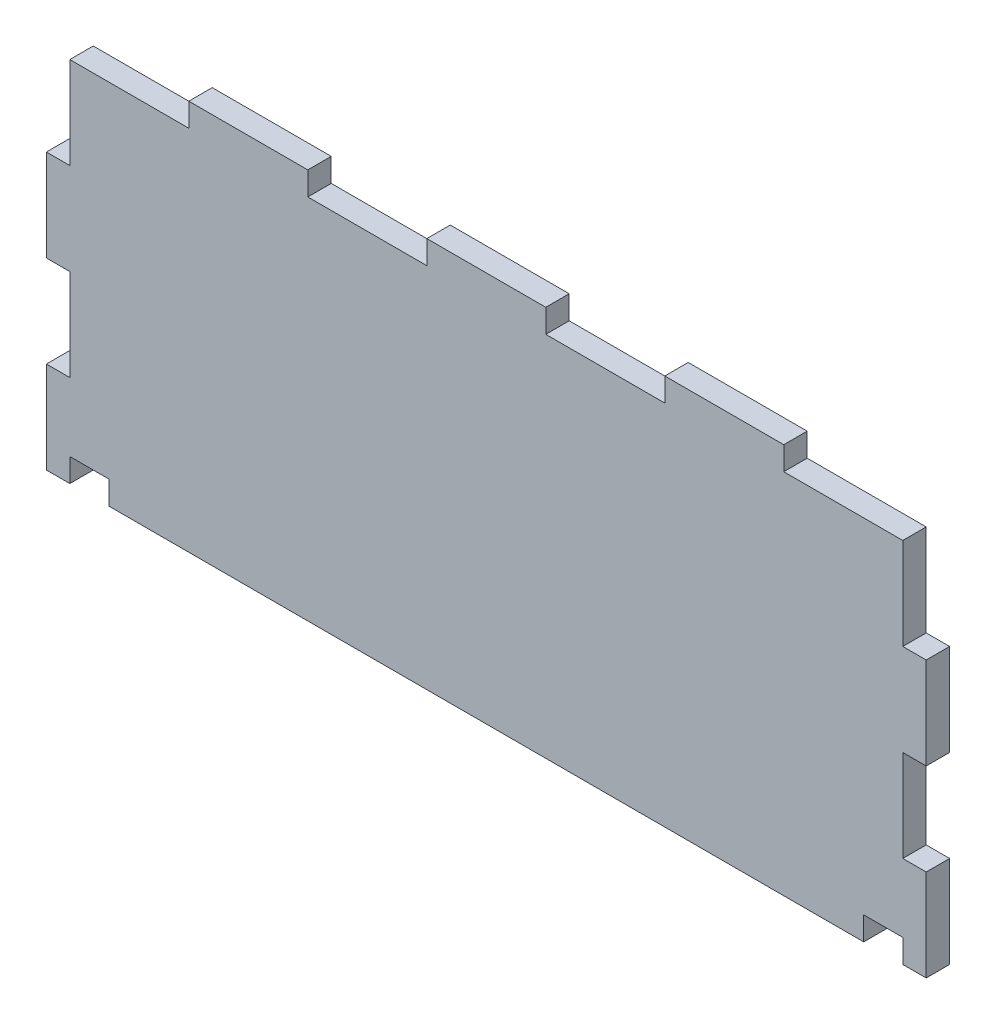
SolidWorks part; units mm, degrees
ref_plane "Alzado" through (0, 0, 0) normal (0, 0, 1) x (1, 0, 0)
ref_plane "Planta" through (0, 0, 0) normal (0, 1, 0) x (1, 0, 0)
ref_plane "Vista lateral" through (0, 0, 0) normal (1, 0, 0) x (0, 0, -1)
sketch "Croquis1" plane through (0, 0, 0) normal (0, 0, 1) x (1, 0, 0)
  line L0 (-76.15, 28.8494) -> (-76.15, -51.02) construction
  line L1 (-79.15, 18.6361) -> (33.46, 18.6361) construction
  line L2 (-79.15, 18.6361) -> (-79.15, -31.3639) construction
  line L3 (-79.15, -31.3639) -> (33.46, -31.3639) construction
  line L4 (33.46, 18.6361) -> (33.46, -31.3639) construction
  line L5 (30.46, 26.8438) -> (30.46, -48.3082) construction
  line L6 (-85.6573, -28.3639) -> (41.9564, -28.3639) construction
  line L7 (-99.0946, 15.6361) -> (68.6346, 15.6361) construction
  line L8 (-71.15, -28.3639) -> (-71.15, -31.3639)
  line L9 (25.46, -28.3639) -> (25.46, -31.3639)
  line L10 (-71.15, -31.3639) -> (25.46, -31.3639)
  line L11 (-71.15, -28.3639) -> (-76.15, -28.3639)
  line L12 (-76.15, -28.3639) -> (-76.15, -31.3639)
  line L13 (-76.15, -31.3639) -> (-79.15, -31.3639)
  line L14 (25.46, -28.3639) -> (30.46, -28.3639)
  line L15 (30.46, -28.3639) -> (30.46, -31.3639)
  line L16 (30.46, -31.3639) -> (33.46, -31.3639)
  line L17 (33.46, -31.3639) -> (33.46, -19.6139)
  line L18 (33.46, -19.6139) -> (30.46, -19.6139)
  line L19 (30.46, -19.6139) -> (30.46, -7.8639)
  line L20 (30.46, -7.8639) -> (33.46, -7.8639)
  line L21 (33.46, -7.8639) -> (33.46, 3.8861)
  line L22 (33.46, 3.8861) -> (30.46, 3.8861)
  line L23 (30.46, 3.8861) -> (30.46, 15.6361)
  line L24 (30.46, 15.6361) -> (15.23, 15.6361)
  line L25 (15.23, 15.6361) -> (15.23, 18.6361)
  line L26 (15.23, 18.6361) -> (0, 18.6361)
  line L27 (0, 18.6361) -> (0, 15.6361)
  line L28 (0, 15.6361) -> (-15.23, 15.6361)
  line L29 (-15.23, 15.6361) -> (-15.23, 18.6361)
  line L30 (-15.23, 18.6361) -> (-30.46, 18.6361)
  line L31 (-30.46, 18.6361) -> (-30.46, 15.6361)
  line L32 (-30.46, 15.6361) -> (-45.69, 15.6361)
  line L33 (-45.69, 15.6361) -> (-45.69, 18.6361)
  line L34 (-45.69, 18.6361) -> (-60.92, 18.6361)
  line L35 (-60.92, 18.6361) -> (-60.92, 15.6361)
  line L36 (-60.92, 15.6361) -> (-76.15, 15.6361)
  line L37 (-79.15, -31.3639) -> (-79.15, -19.6139)
  line L38 (-79.15, -19.6139) -> (-76.15, -19.6139)
  line L39 (-76.15, -19.6139) -> (-76.15, -7.8639)
  line L40 (-76.15, -7.8639) -> (-79.15, -7.8639)
  line L41 (-79.15, -7.8639) -> (-79.15, 3.8861)
  line L42 (-79.15, 3.8861) -> (-76.15, 3.8861)
  line L43 (-76.15, 3.8861) -> (-76.15, 15.6361)
  line L44 (138.6179, 261.633) -> (138.6179, -48.3185) construction
  line L45 (141.6179, 35.2642) -> (141.6179, -48.3185) construction
  line L46 (243.2279, 33.3064) -> (243.2279, -51.0303) construction
  line L47 (246.2279, 143.2673) -> (246.2279, -57.2157) construction
  line L48 (243.2279, -31.3639) -> (141.6179, -31.3639)
  line L49 (141.6179, -31.3639) -> (141.6179, -19.6139)
  line L50 (141.6179, -19.6139) -> (138.6179, -19.6139)
  line L51 (138.6179, -19.6139) -> (138.6179, -6.5272)
  line L52 (138.6179, -6.5272) -> (141.6179, -6.5272)
  line L53 (141.6179, -6.5272) -> (141.6179, 3.8861)
  line L54 (141.6179, 3.8861) -> (138.6179, 3.8861)
  line L55 (138.6179, 3.8861) -> (138.6179, 18.6361)
  line L56 (109.4401, 103.7223) -> (113.3913, 103.7223) construction
  line L57 (138.6179, 211.3323) -> (-4.8813, 211.3323) construction
  line L58 (243.2279, -31.3639) -> (243.2279, -19.6139)
  line L59 (-76.15, 208.3323) -> (30.46, 208.3323) construction
  line L60 (-76.15, 208.3321) -> (-76.15, 106.7221) construction
  line L61 (-76.15, 106.7223) -> (30.46, 106.7223) construction
  line L62 (30.46, 208.3321) -> (30.46, 106.7221) construction
  line L63 (243.2279, -19.6139) -> (246.2279, -19.6139)
  line L64 (246.2279, -19.6139) -> (246.2279, -6.5272)
  line L65 (246.2279, -6.5272) -> (243.2279, -6.5272)
  line L66 (243.2279, -6.5272) -> (243.2279, 3.8861)
  line L67 (243.2279, 3.8861) -> (246.2279, 3.8861)
  line L68 (246.2279, 3.8861) -> (246.2279, 18.6361)
  line L69 (138.6179, 18.6361) -> (153.9908, 18.6361)
  line L70 (153.9908, 18.6361) -> (153.9908, 15.6361)
  line L71 (153.9908, 15.6361) -> (169.3636, 15.6361)
  line L72 (169.3636, 15.6361) -> (169.3636, 18.6361)
  line L73 (169.3636, 18.6361) -> (184.7365, 18.6361)
  line L74 (184.7365, 18.6361) -> (184.7365, 15.6361)
  line L75 (184.7365, 15.6361) -> (200.1093, 15.6361)
  line L76 (200.1093, 15.6361) -> (200.1093, 18.6361)
  line L77 (200.1093, 18.6361) -> (215.4822, 18.6361)
  line L78 (215.4822, 18.6361) -> (215.4822, 15.6361)
  line L79 (215.4822, 15.6361) -> (230.855, 15.6361)
  line L80 (230.855, 15.6361) -> (230.855, 18.6361)
  line L81 (230.855, 18.6361) -> (246.2279, 18.6361)
  line L82 (138.6179, 195.9594) -> (-142.1003, 195.9594) construction
  line L83 (138.6179, 180.5865) -> (-142.1003, 180.5865) construction
  line L84 (138.6179, 165.2137) -> (-133.8306, 165.2137) construction
  line L85 (138.6179, 149.8408) -> (-118.3699, 149.8408) construction
  line L86 (138.6179, 134.468) -> (-142.1003, 134.468) construction
  line L87 (138.6179, 119.0951) -> (-118.3699, 119.0951) construction
  line L88 (30.46, 103.7223) -> (30.46, 119.0951)
  line L89 (30.46, 119.0951) -> (33.46, 119.0951)
  line L90 (33.46, 119.0951) -> (33.46, 134.468)
  line L91 (33.46, 134.468) -> (30.46, 134.468)
  line L92 (30.46, 134.468) -> (30.46, 149.8408)
  line L93 (30.46, 149.8408) -> (33.46, 149.8408)
  line L94 (33.46, 149.8408) -> (33.46, 165.2137)
  line L95 (33.46, 165.2137) -> (30.46, 165.2137)
  line L96 (30.46, 165.2137) -> (30.46, 180.5865)
  line L97 (30.46, 180.5865) -> (33.46, 180.5865)
  line L98 (33.46, 180.5865) -> (33.46, 195.9594)
  line L99 (33.46, 195.9594) -> (30.46, 195.9594)
  line L100 (30.46, 195.9594) -> (30.46, 211.3323)
  line L101 (230.855, 18.6361) -> (230.855, 103.7223) construction
  line L102 (215.4822, 18.6361) -> (215.4822, 103.7223) construction
  line L103 (200.1093, 18.6361) -> (200.1093, 103.7223) construction
  line L104 (184.7365, 18.6361) -> (184.7365, 103.7223) construction
  line L105 (169.3636, 18.6361) -> (169.3636, 103.7223) construction
  line L106 (153.9908, 18.6361) -> (153.9908, 103.7223) construction
  line L107 (15.23, 106.7223) -> (30.46, 106.7223)
  line L108 (15.23, 103.7223) -> (15.23, 106.7223)
  line L109 (15.23, 103.7223) -> (0, 103.7223)
  line L110 (0, 103.7223) -> (0, 106.7223)
  line L111 (0, 106.7223) -> (-15.23, 106.7223)
  line L112 (-15.23, 106.7223) -> (-15.23, 103.7223)
  line L113 (-15.23, 103.7223) -> (-30.46, 103.7223)
  line L114 (-30.46, 103.7223) -> (-30.46, 106.7223)
  line L115 (-30.46, 106.7223) -> (-45.69, 106.7223)
  line L116 (-45.69, 106.7223) -> (-45.69, 103.7223)
  line L117 (-45.69, 103.7223) -> (-60.92, 103.7223)
  line L118 (-60.92, 103.7223) -> (-60.92, 106.7223)
  line L119 (-60.92, 106.7223) -> (-76.15, 106.7223)
  line L120 (-76.15, 106.7223) -> (-76.15, 119.0951)
  line L121 (-76.15, 119.0951) -> (-79.15, 119.0951)
  line L122 (-79.15, 119.0951) -> (-79.15, 134.468)
  line L123 (-79.15, 134.468) -> (-76.15, 134.468)
  line L124 (-76.15, 134.468) -> (-76.15, 149.8408)
  line L125 (-76.15, 149.8408) -> (-79.15, 149.8408)
  line L126 (-79.15, 149.8408) -> (-79.15, 165.2137)
  line L127 (-79.15, 165.2137) -> (-76.15, 165.2137)
  line L128 (-76.15, 165.2137) -> (-76.15, 180.5865)
  line L129 (-76.15, 180.5865) -> (-79.15, 180.5865)
  line L130 (-79.15, 180.5865) -> (-79.15, 195.9594)
  line L131 (-79.15, 195.9594) -> (-76.15, 195.9594)
  line L132 (-76.15, 195.9594) -> (-76.15, 208.3323)
  line L133 (-76.15, 208.3323) -> (-60.92, 208.3323)
  line L134 (-60.92, 208.3323) -> (-60.92, 211.3323)
  line L135 (-60.92, 211.3323) -> (-45.69, 211.3323)
  line L136 (-45.69, 211.3323) -> (-45.69, 208.3323)
  line L137 (-45.69, 208.3323) -> (-30.46, 208.3323)
  line L138 (-30.46, 208.3323) -> (-30.46, 211.3323)
  line L139 (-30.46, 211.3323) -> (-15.23, 211.3323)
  line L140 (-15.23, 211.3323) -> (-15.23, 208.3323)
  line L141 (-15.23, 208.3323) -> (0, 208.3323)
  line L142 (0, 208.3323) -> (0, 211.3323)
  line L143 (0, 211.3323) -> (15.23, 211.3323)
  line L144 (15.23, 211.3323) -> (15.23, 208.3323)
  line L145 (15.23, 208.3323) -> (30.46, 208.3323)
  line L146 (30.46, 106.7223) -> (30.46, 119.0951)
  arc A0 (246.2279, 103.7223) -> (138.6179, 211.3323) centre (138.6179, 103.7223) ccw construction
  arc A1 (230.855, 103.7223) -> (138.6179, 195.9594) centre (138.6179, 103.7223) ccw construction
  arc A2 (215.4822, 103.7223) -> (138.6179, 180.5865) centre (138.6179, 103.7223) ccw construction
  arc A3 (200.1093, 103.7223) -> (138.6179, 165.2137) centre (138.6179, 103.7223) ccw construction
  arc A4 (184.7365, 103.7223) -> (138.6179, 149.8408) centre (138.6179, 103.7223) ccw construction
  arc A5 (169.3636, 103.7223) -> (138.6179, 134.468) centre (138.6179, 103.7223) ccw construction
  arc A6 (153.9908, 103.7223) -> (138.6179, 119.0951) centre (138.6179, 103.7223) ccw construction
  dimension "D1" = 112.61
  dimension "D2" = 3
  dimension "D3" = 3
  dimension "D4" = 3
  dimension "D5" = 3
  dimension "D6" = 3
  dimension "D7" = 5
  dimension "D8" = 5
  dimension "D9" = 3
  dimension "D10" = 3
  dimension "D11" = 107.61
  dimension "D12" = 3
  dimension "D13" = 3
  dimension "D14" = 3
extrude "Saliente-Extruir1" add sketch "Croquis1" along normal blind 3 contours L43 L42 L41 L40 L39 L38 L37 L13 L12 L11 L8 L10 L9 L14 L15 L16 L17 L18 L19 L20 L21 L22 L23 L24 L25 L26 L27 L28 L29 L30 L31 L32 L33 L34 L35 L36
